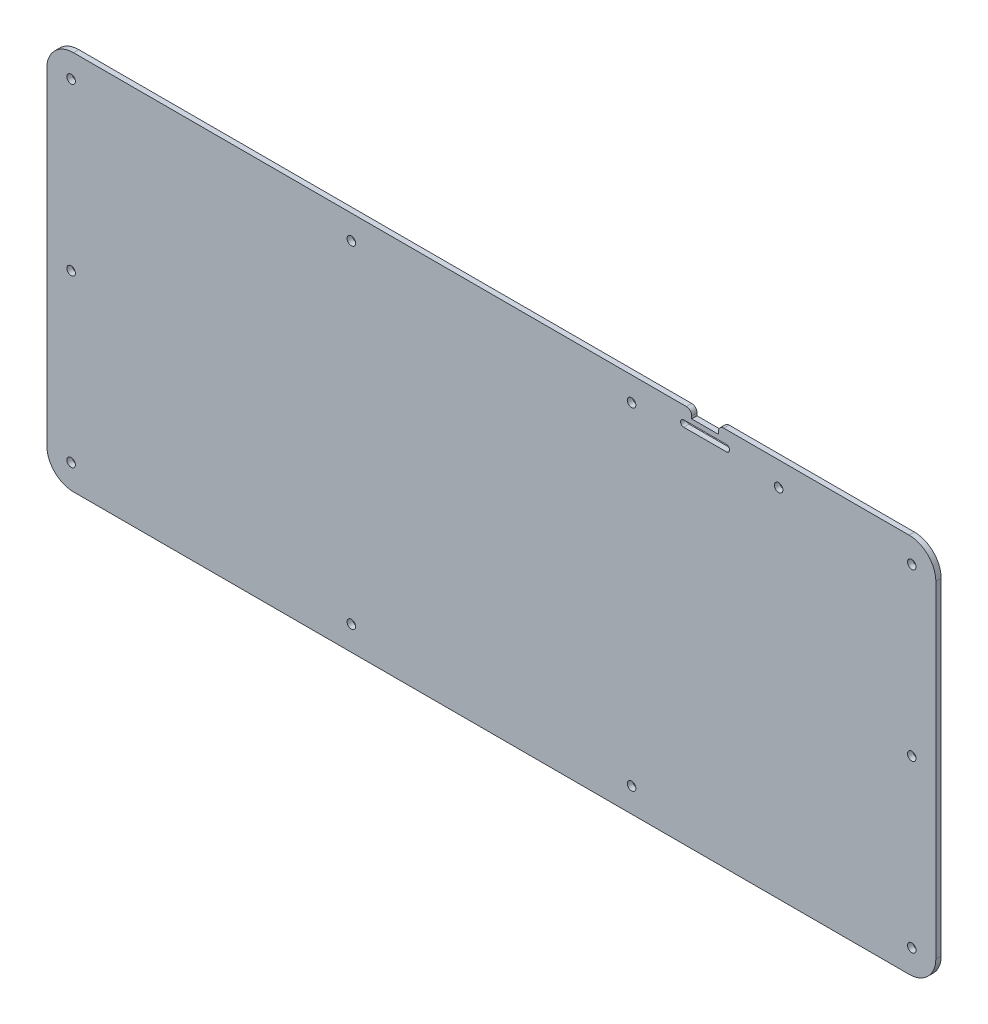
SolidWorks part; units mm, degrees
ref_plane "前视基准面" through (0, 0, 0) normal (0, 0, 1) x (1, 0, 0)
ref_plane "上视基准面" through (0, 0, 0) normal (0, 1, 0) x (1, 0, 0)
ref_plane "右视基准面" through (0, 0, 0) normal (1, 0, 0) x (0, 0, -1)
sketch "草图1" plane through (0, 0, 0) normal (0, 0, 1) x (1, 0, 0)
  line L0 (-165.1585, 77.4336) -> (-165.1585, -44.9994)
  line L1 (-155.1585, -54.9994) -> (157.7385, -54.9994)
  line L2 (167.7385, 77.4336) -> (167.7385, -44.9994)
  line L3 (-153.1585, 75.4336) -> (155.7385, 75.4336) construction
  line L4 (-153.1585, 75.4336) -> (-153.1585, -42.9994) construction
  line L5 (-153.1585, -42.9994) -> (155.7385, -42.9994) construction
  line L6 (155.7385, 75.4336) -> (155.7385, -42.9994) construction
  line L7 (-155.1585, 87.4336) -> (74.3375, 87.4336)
  line L8 (73.3375, 81.4336) -> (89.3375, 81.4336) construction
  line L9 (73.3375, 82.6336) -> (89.3375, 82.6336)
  line L10 (73.3375, 80.2336) -> (89.3375, 80.2336)
  line L11 (76.3375, 85.4336) -> (76.3375, 84.4336)
  line L12 (76.3375, 84.4336) -> (86.3375, 84.4336)
  line L13 (86.3375, 85.4336) -> (86.3375, 84.4336)
  line L14 (88.3375, 87.4336) -> (157.7385, 87.4336)
  line L15 (161.7385, 81.4336) -> (161.7385, -48.9994) construction
  line L16 (161.7385, -48.9994) -> (-159.1585, -48.9994) construction
  line L17 (-159.1585, -48.9994) -> (-159.1585, 81.4336) construction
  line L18 (-159.1585, 81.4336) -> (161.7385, 81.4336) construction
  circle A0 centre (53.8035, 78.4336) radius 1.6
  circle A1 centre (108.8715, 78.4336) radius 1.6
  circle A2 centre (158.7385, 78.4336) radius 1.6
  circle A3 centre (158.7385, 16.2825) radius 1.5998
  circle A4 centre (158.7385, -45.8685) radius 1.5999
  circle A5 centre (53.8035, -45.8685) radius 1.5999
  circle A6 centre (-51.1295, -45.8685) radius 1.5999
  circle A7 centre (-156.0634, -45.8685) radius 1.5999
  circle A8 centre (-156.0634, 16.2825) radius 1.5998
  circle A9 centre (-156.0634, 78.4336) radius 1.6
  circle A10 centre (-51.1295, 78.4336) radius 1.6
  arc A11 (157.7385, 87.4336) -> (167.7385, 77.4336) centre (157.7385, 77.4336) cw
  arc A12 (157.7385, -54.9994) -> (167.7385, -44.9994) centre (157.7385, -44.9994) ccw
  arc A13 (-165.1585, -44.9994) -> (-155.1585, -54.9994) centre (-155.1585, -44.9994) ccw
  arc A14 (-155.1585, 87.4336) -> (-165.1585, 77.4336) centre (-155.1585, 77.4336) ccw
  arc A15 (73.3375, 82.6336) -> (73.3375, 80.2336) centre (73.3375, 81.4336) ccw
  arc A16 (89.3375, 80.2336) -> (89.3375, 82.6336) centre (89.3375, 81.4336) ccw
  arc A17 (88.3375, 87.4336) -> (86.3375, 85.4336) centre (88.3375, 85.4336) ccw
  arc A18 (74.3375, 87.4336) -> (76.3375, 85.4336) centre (74.3375, 85.4336) cw
  point P21 (81.3375, 81.4336)
  point P29 (81.3375, 84.4336)
  dimension "D1" = 3.2
  dimension "D6" = 10
  dimension "D13" = 2
  dimension "D2" = 55.068
  dimension "D3" = 6
  dimension "D4" = 6
  dimension "D5" = 6
  dimension "D7" = 6
  dimension "D8" = 6
  dimension "D9" = 6
  dimension "D10" = 6
  dimension "D11" = 10
  dimension "D12" = 16
extrude "凸台-拉伸2" add sketch "草图1" along normal blind 2 contours L7 A18 L11 L12 L13 A17 L14 A11 L2 A12 L1 A13 L0 A14 | L10 A16 L9 A15 | A1 | A2 | A3 | A4 | A5 | A6 | A7 | A8 | A9 | A10 | A0
